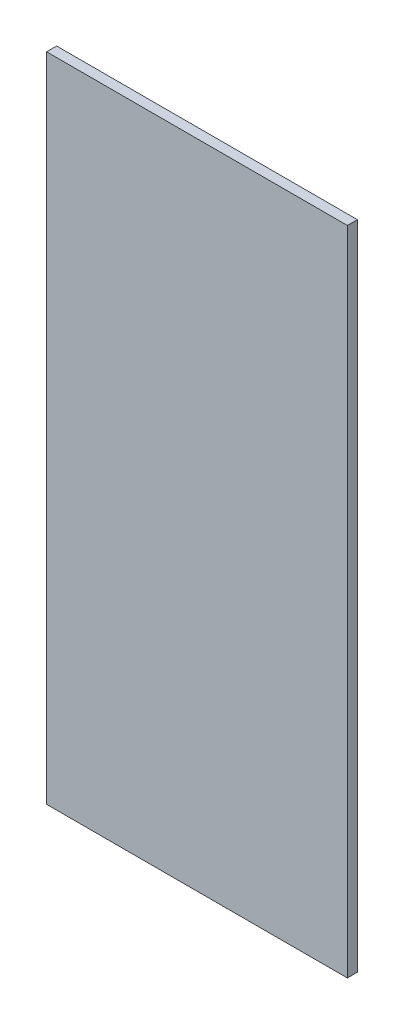
SolidWorks part; units mm, degrees
ref_plane "Front Plane" through (0, 0, 0) normal (0, 0, 1) x (1, 0, 0)
ref_plane "Top Plane" through (0, 0, 0) normal (0, 1, 0) x (1, 0, 0)
ref_plane "Right Plane" through (0, 0, 0) normal (1, 0, 0) x (0, 0, -1)
sketch "Sketch1" plane through (0, 0, 0) normal (0, 0, 1) x (1, 0, 0)
  line L0 (0, 0) -> (-38.1, 0)
  line L1 (-38.1, 0) -> (-38.1, 82.55)
  line L2 (-38.1, 82.55) -> (0, 82.55)
  line L3 (0, 82.55) -> (0, 0)
extrude "Boss-Extrude1" add sketch "Sketch1" along normal blind 1.27
